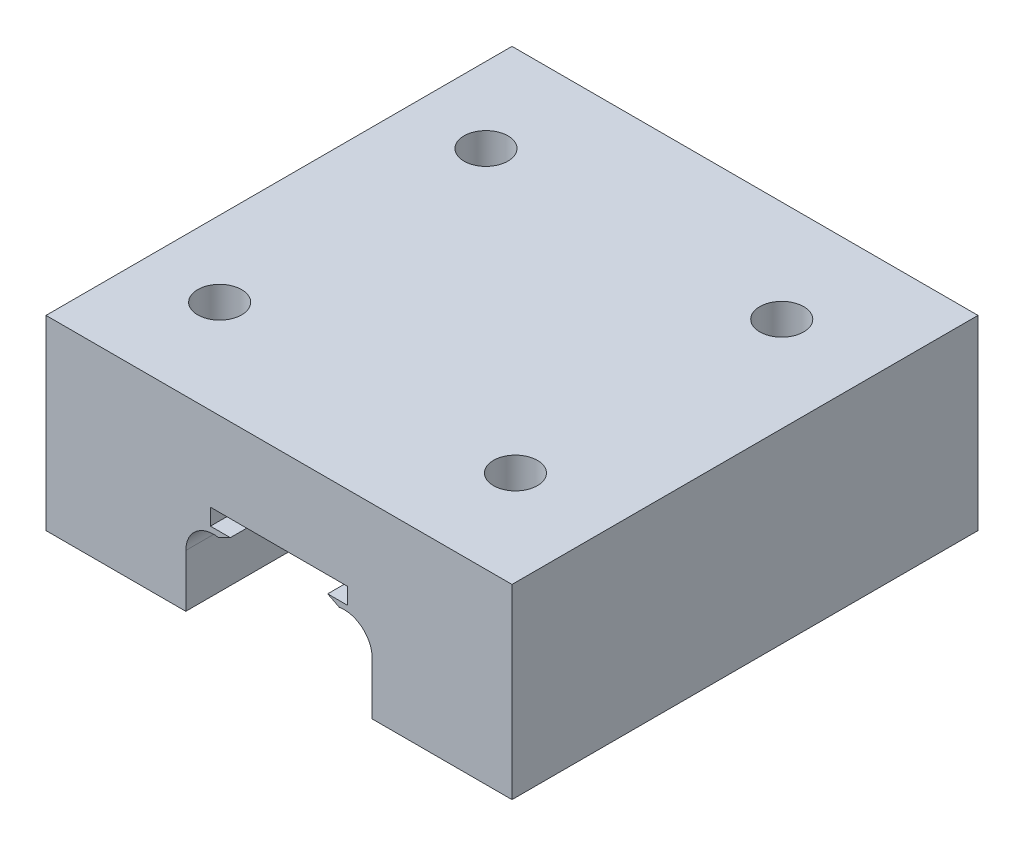
SolidWorks part; units mm, degrees
ref_plane "Alzado" through (0, 0, 0) normal (0, 0, 1) x (1, 0, 0)
ref_plane "Planta" through (0, 0, 0) normal (0, 1, 0) x (1, 0, 0)
ref_plane "Vista lateral" through (0, 0, 0) normal (1, 0, 0) x (0, 0, -1)
sketch "Croquis1" plane through (0, 0, 0) normal (0, 0, 1) x (1, 0, 0)
  line L0 (-10, 0) -> (-10, 5.6561)
  line L1 (-25, 0) -> (-10, 0)
  line L2 (-25, 0) -> (-25, 20)
  line L3 (-25, 20) -> (25, 20)
  line L4 (25, 0) -> (25, 20)
  line L5 (10, 0) -> (10, 5.6561)
  line L6 (-6.4615, 8.6073) -> (-5.2217, 9.2369)
  line L7 (-5.2217, 9.2369) -> (-7.3548, 9.2369)
  line L8 (-7.3548, 9.2369) -> (-7.3548, 11)
  line L9 (-7.3548, 11) -> (7.3548, 11)
  line L10 (0, 11) -> (0, 0) construction
  line L11 (6.4615, 8.6073) -> (5.2217, 9.2369)
  line L12 (5.2217, 9.2369) -> (7.3548, 9.2369)
  line L13 (7.3548, 9.2369) -> (7.3548, 11)
  line L14 (10, 0) -> (25, 0)
  line L15 (-10, 0) -> (0, 0) construction
  line L16 (0, 0) -> (10, 0) construction
  arc A0 (-10, 5.6561) -> (-6.4615, 8.6073) centre (-7, 5.6561) cw
  arc A1 (10, 5.6561) -> (6.4615, 8.6073) centre (7, 5.6561) ccw
  dimension "D3" = 3
  dimension "D1" = 50
  dimension "D2" = 20
  dimension "D4" = 15
  dimension "D5" = 11
extrude "Saliente-Extruir1" add sketch "Croquis1" along normal blind 50 contours L3 L4 L14 L5 A1 L11 L12 L13 L9 L8 L7 L6 A0 L0 L1 L2
sketch "Croquis2" plane through (0, 20, 0) normal (0, 1, 0) x (1, 0, 0)
  circle A0 centre (14.8319, -10.8891) radius 2.3567
  circle A1 centre (14.8319, -39.4618) radius 2.3567
  circle A2 centre (-16.9044, -39.4618) radius 2.3567
  circle A3 centre (-16.9044, -10.8891) radius 2.3567
extrude "Cortar-Extruir1" cut sketch "Croquis2" against normal blind 20
